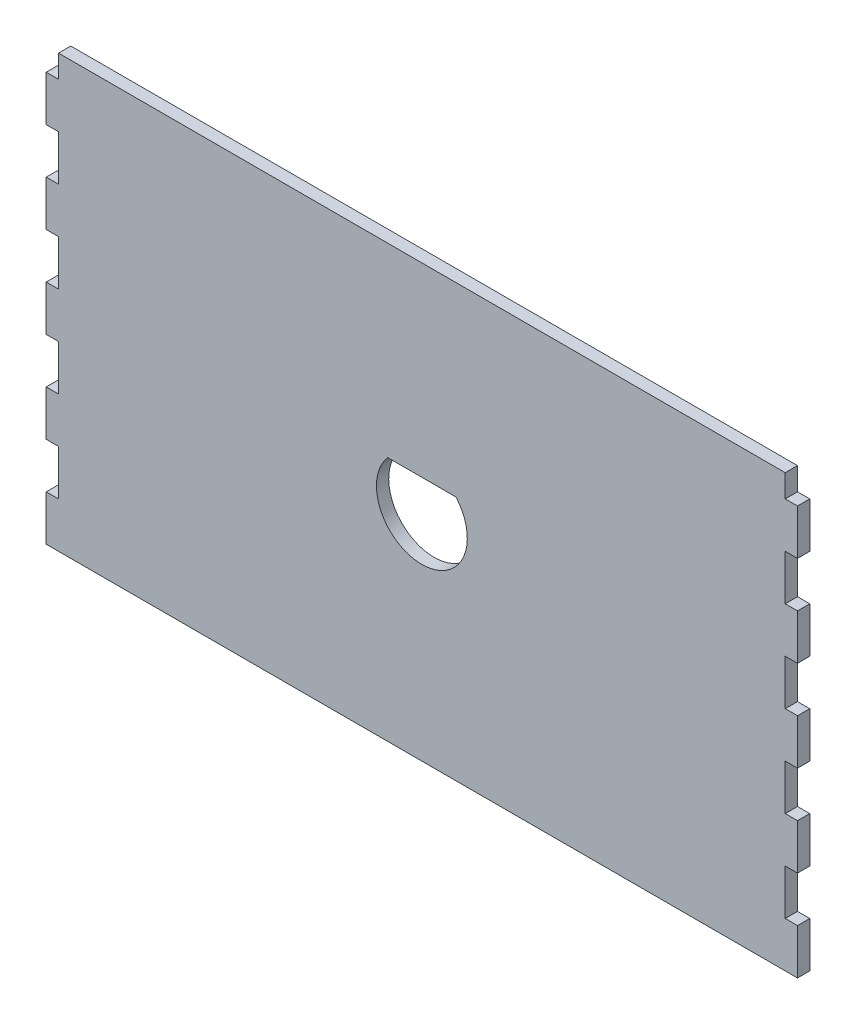
SolidWorks part; units mm, degrees
material "Maple"
ref_plane "Front Plane" through (0, 0, 0) normal (0, 0, 1) x (1, 0, 0)
ref_plane "Top Plane" through (0, 0, 0) normal (0, 1, 0) x (1, 0, 0)
ref_plane "Right Plane" through (0, 0, 0) normal (1, 0, 0) x (0, 0, -1)
sketch "Sketch1" plane through (0, 0, 0) normal (0, 0, 1) x (1, 0, 0)
  line L0 (0, 47.5) -> (0, -47.5) construction
  line L1 (-80, -47.5) -> (80, -47.5)
  line L2 (-80, -37.5) -> (-80, -27.5)
  line L3 (-80, 47.5) -> (80, 47.5)
  line L4 (80, -37.5) -> (80, -27.5)
  line L5 (-80, -47.5) -> (80, 47.5) construction
  line L6 (-80, 47.5) -> (80, -47.5) construction
  line L8 (80, -47.5) -> (82.7, -47.5)
  line L10 (80, -37.5) -> (82.7, -37.5)
  line L11 (82.7, -47.5) -> (82.7, -37.5)
  line L12 (80, -47.5) -> (82.7, -37.5) construction
  line L13 (80, -37.5) -> (82.7, -47.5) construction
  line L14 (-80, -47.5) -> (-82.7, -37.5) construction
  line L15 (-80, -37.5) -> (-82.7, -47.5) construction
  line L16 (-80, -47.5) -> (-82.7, -47.5)
  line L17 (-82.7, -47.5) -> (-82.7, -37.5)
  line L18 (-80, -37.5) -> (-82.7, -37.5)
  line L19 (80, -17.5) -> (82.7, -17.5)
  line L20 (82.7, -27.5) -> (82.7, -17.5)
  line L21 (80, -27.5) -> (82.7, -27.5)
  line L22 (80, 2.5) -> (82.7, 2.5)
  line L23 (82.7, -7.5) -> (82.7, 2.5)
  line L24 (80, -7.5) -> (82.7, -7.5)
  line L25 (80, 22.5) -> (82.7, 22.5)
  line L26 (82.7, 12.5) -> (82.7, 22.5)
  line L27 (80, 12.5) -> (82.7, 12.5)
  line L28 (80, 42.5) -> (82.7, 42.5)
  line L29 (82.7, 32.5) -> (82.7, 42.5)
  line L30 (80, 32.5) -> (82.7, 32.5)
  line L31 (80, -37.5) -> (80, -27.5) construction
  line L32 (80, -17.5) -> (82.7, -17.5)
  line L33 (82.7, -27.5) -> (82.7, -17.5)
  line L34 (80, -27.5) -> (82.7, -27.5)
  line L35 (-80, -17.5) -> (-82.7, -17.5)
  line L36 (-82.7, -27.5) -> (-82.7, -17.5)
  line L37 (-80, -27.5) -> (-82.7, -27.5)
  line L38 (80, 2.5) -> (82.7, 2.5)
  line L39 (82.7, -7.5) -> (82.7, 2.5)
  line L40 (80, -7.5) -> (82.7, -7.5)
  line L41 (-80, 2.5) -> (-82.7, 2.5)
  line L42 (-82.7, -7.5) -> (-82.7, 2.5)
  line L43 (-80, -7.5) -> (-82.7, -7.5)
  line L44 (80, 22.5) -> (82.7, 22.5)
  line L45 (82.7, 12.5) -> (82.7, 22.5)
  line L46 (80, 12.5) -> (82.7, 12.5)
  line L47 (-80, 22.5) -> (-82.7, 22.5)
  line L48 (-82.7, 12.5) -> (-82.7, 22.5)
  line L49 (-80, 12.5) -> (-82.7, 12.5)
  line L50 (80, 42.5) -> (82.7, 42.5)
  line L51 (82.7, 32.5) -> (82.7, 42.5)
  line L52 (80, 32.5) -> (82.7, 32.5)
  line L53 (-80, 42.5) -> (-82.7, 42.5)
  line L54 (-82.7, 32.5) -> (-82.7, 42.5)
  line L55 (-80, 32.5) -> (-82.7, 32.5)
  line L56 (80, -37.5) -> (80, -27.5) construction
  line L57 (-80, 42.5) -> (-80, 47.5)
  line L58 (-80, 22.5) -> (-80, 32.5)
  line L59 (-80, 2.5) -> (-80, 12.5)
  line L60 (-80, -17.5) -> (-80, -7.5)
  line L61 (80, 42.5) -> (80, 47.5)
  line L62 (80, 22.5) -> (80, 32.5)
  line L63 (80, 2.5) -> (80, 12.5)
  line L64 (80, -17.5) -> (80, -7.5)
  line L65 (-7.5, 6.6144) -> (7.5, 6.6144)
  arc A0 (-7.5, 6.6144) -> (7.5, 6.6144) centre (0, 0) ccw
  point P0 (0, 0)
  point P11 (81.35, -42.5)
  point P15 (-81.35, -42.5)
  dimension "D9" = 10
  dimension "D1" = 160
  dimension "D2" = 95
  dimension "D3" = 2.7
  dimension "D4" = 10
  dimension "D5" = 5
  dimension "D6" = 10
  dimension "D8" = 10
  dimension "D10" = 15
  dimension "D7" = 5
extrude "Boss-Extrude1" add sketch "Sketch1" along normal blind 2.7 contours L19 L64 L24 L23 L22 L63 L27 L26 L25 L62 L30 L29 L28 L61 L3 L57 L53 L54 L55 L58 L47 L48 L49 L59 L41 L42 L43 L60 L35 L36 L37 L2 L18 L17 L16 L1 L8 L11 L10 L4 L21 L20 A0 L65
